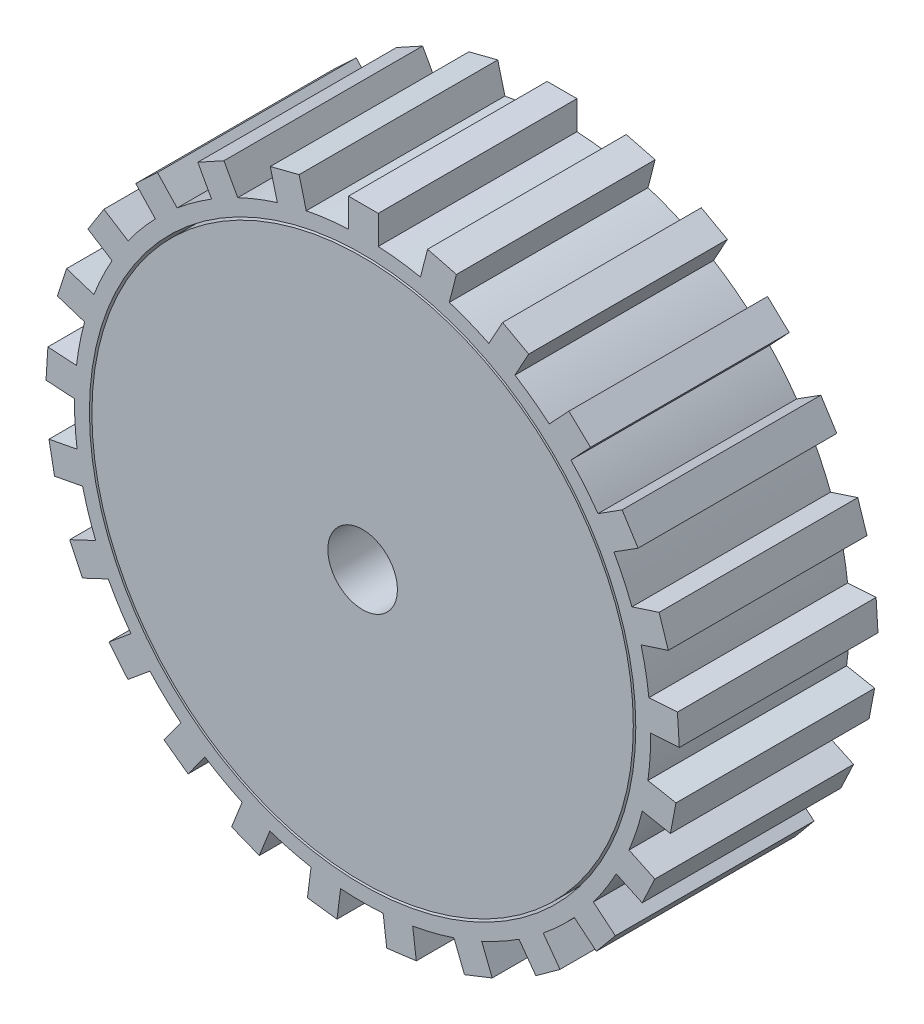
SolidWorks part; units mm, degrees
ref_plane "Front Plane" through (0, 0, 0) normal (0, 0, 1) x (1, 0, 0)
ref_plane "Top Plane" through (0, 0, 0) normal (0, 1, 0) x (1, 0, 0)
ref_plane "Right Plane" through (0, 0, 0) normal (1, 0, 0) x (0, 0, -1)
sketch "Sketch1" plane through (0, 0, 0) normal (0, 0, 1) x (1, 0, 0)
  line L0 (-1.4243, 28.965) -> (-1.4243, 31.8414)
  line L1 (-1.4243, 31.8414) -> (1.5757, 31.8414)
  line L2 (1.5757, 31.8414) -> (1.5757, 28.9572)
  line L3 (9.4448, 30.4492) -> (8.7275, 27.6556)
  line L4 (6.5391, 31.1953) -> (9.4448, 30.4492)
  line L5 (5.8237, 28.4092) -> (6.5391, 31.1953)
  line L6 (16.7205, 27.1438) -> (15.331, 24.6163)
  line L7 (14.0916, 28.589) -> (16.7205, 27.1438)
  line L8 (12.7058, 26.0684) -> (14.0916, 28.589)
  line L9 (22.9456, 22.1328) -> (20.9712, 20.0302)
  line L10 (20.7587, 24.1864) -> (22.9456, 22.1328)
  line L11 (18.7896, 22.0896) -> (20.7587, 24.1864)
  line L12 (27.7289, 15.7311) -> (25.2936, 14.1856)
  line L13 (26.1214, 18.2641) -> (27.7289, 15.7311)
  line L14 (23.6928, 16.7228) -> (26.1214, 18.2641)
  line L15 (30.7699, 8.341) -> (28.0268, 7.4497)
  line L16 (29.8429, 11.1942) -> (30.7699, 8.341)
  line L17 (27.1072, 10.3053) -> (29.8429, 11.1942)
  line L18 (31.8775, 0.4268) -> (28.999, 0.2457)
  line L19 (31.6892, 3.4209) -> (31.8775, 0.4268)
  line L20 (28.8184, 3.2403) -> (31.6892, 3.4209)
  line L21 (30.9822, -7.5142) -> (28.149, -6.9738)
  line L22 (31.5443, -4.5674) -> (30.9822, -7.5142)
  line L23 (28.7188, -4.0284) -> (31.5443, -4.5674)
  line L24 (28.1401, -14.9831) -> (25.5303, -13.7551)
  line L25 (29.4174, -12.2686) -> (28.1401, -14.9831)
  line L26 (26.8148, -11.0439) -> (29.4174, -12.2686)
  line L27 (23.5299, -21.5106) -> (21.3075, -19.6721)
  line L28 (25.4421, -19.199) -> (23.5299, -21.5106)
  line L29 (23.2258, -17.3655) -> (25.4421, -19.199)
  line L30 (17.4412, -26.6864) -> (15.7459, -24.353)
  line L31 (19.8682, -24.923) -> (17.4412, -26.6864)
  line L32 (18.1775, -22.596) -> (19.8682, -24.923)
  line L33 (10.2566, -30.1854) -> (9.1948, -27.5037)
  line L34 (13.0459, -29.0811) -> (10.2566, -30.1854)
  line L35 (11.987, -26.4066) -> (13.0459, -29.0811)
  line L36 (2.4275, -31.7878) -> (2.0661, -28.9263)
  line L37 (5.4039, -31.4118) -> (2.4275, -31.7878)
  line L38 (5.0434, -28.5581) -> (5.4039, -31.4118)
  line L39 (-5.554, -31.3929) -> (-5.1925, -28.5313)
  line L40 (-2.5777, -31.7689) -> (-5.554, -31.3929)
  line L41 (-2.2172, -28.9151) -> (-2.5777, -31.7689)
  line L42 (-13.1866, -29.0254) -> (-12.1249, -26.3436)
  line L43 (-10.3973, -30.1297) -> (-13.1866, -29.0254)
  line L44 (-9.3384, -27.4553) -> (-10.3973, -30.1297)
  line L45 (-19.9907, -24.8341) -> (-18.2953, -22.5007)
  line L46 (-17.5636, -26.5975) -> (-19.9907, -24.8341)
  line L47 (-15.8729, -24.2704) -> (-17.5636, -26.5975)
  line L48 (-25.5386, -19.0824) -> (-23.3162, -17.2439)
  line L49 (-23.6263, -21.394) -> (-25.5386, -19.0824)
  line L50 (-21.41, -19.5605) -> (-23.6263, -21.394)
  line L51 (-29.4819, -12.1317) -> (-26.8721, -10.9037)
  line L52 (-28.2045, -14.8462) -> (-29.4819, -12.1317)
  line L53 (-25.6019, -13.6215) -> (-28.2045, -14.8462)
  line L54 (-31.5727, -4.4187) -> (-28.7395, -3.8783)
  line L55 (-31.0105, -7.3656) -> (-31.5727, -4.4187)
  line L56 (-28.1851, -6.8266) -> (-31.0105, -7.3656)
  line L57 (-31.6797, 3.5719) -> (-28.8011, 3.3908)
  line L58 (-31.868, 0.5778) -> (-31.6797, 3.5719)
  line L59 (-28.9973, 0.3972) -> (-31.868, 0.5778)
  line L60 (-29.7961, 11.3381) -> (-27.053, 10.4468)
  line L61 (-30.7231, 8.4849) -> (-29.7961, 11.3381)
  line L62 (-27.9875, 7.5961) -> (-30.7231, 8.4849)
  line L63 (-26.0403, 18.3919) -> (-23.6051, 16.8464)
  line L64 (-27.6478, 15.8589) -> (-26.0403, 18.3919)
  line L65 (-25.2192, 14.3176) -> (-27.6478, 15.8589)
  line L66 (-20.6483, 24.29) -> (-18.6739, 22.1875)
  line L67 (-22.8353, 22.2364) -> (-20.6483, 24.29)
  line L68 (-20.8662, 20.1396) -> (-22.8353, 22.2364)
  line L69 (-13.959, 28.6619) -> (-12.5695, 26.1344)
  line L70 (-16.5879, 27.2167) -> (-13.959, 28.6619)
  line L71 (-15.2022, 24.696) -> (-16.5879, 27.2167)
  line L72 (-6.3925, 31.2329) -> (-5.6752, 28.4393)
  line L73 (-9.2982, 30.4868) -> (-6.3925, 31.2329)
  line L74 (-8.5829, 27.7008) -> (-9.2982, 30.4868)
  circle A0 centre (0, 0) radius 27.5
  arc A1 (-15.2022, 24.696) -> (-18.6739, 22.1875) centre (0, 0) ccw
  arc A2 (-20.8662, 20.1396) -> (-23.6051, 16.8464) centre (0, 0) ccw
  arc A3 (-25.2192, 14.3176) -> (-27.053, 10.4468) centre (0, 0) ccw
  arc A4 (-8.5829, 27.7008) -> (-12.5695, 26.1344) centre (0, 0) ccw
  arc A5 (-1.4243, 28.965) -> (-5.6752, 28.4393) centre (0, 0) ccw
  arc A6 (5.8237, 28.4092) -> (1.5757, 28.9572) centre (0, 0) ccw
  arc A7 (12.7058, 26.0684) -> (8.7275, 27.6556) centre (0, 0) ccw
  arc A8 (18.7896, 22.0896) -> (15.331, 24.6163) centre (0, 0) ccw
  arc A9 (23.6928, 16.7228) -> (20.9712, 20.0302) centre (0, 0) ccw
  arc A10 (27.1072, 10.3053) -> (25.2936, 14.1856) centre (0, 0) ccw
  arc A11 (28.8184, 3.2403) -> (28.0268, 7.4497) centre (0, 0) ccw
  arc A12 (28.7188, -4.0284) -> (28.999, 0.2457) centre (0, 0) ccw
  arc A13 (26.8148, -11.0439) -> (28.149, -6.9738) centre (0, 0) ccw
  arc A14 (23.2258, -17.3655) -> (25.5303, -13.7551) centre (0, 0) ccw
  arc A15 (18.1775, -22.596) -> (21.3075, -19.6721) centre (0, 0) ccw
  arc A16 (11.987, -26.4066) -> (15.7459, -24.353) centre (0, 0) ccw
  arc A17 (5.0434, -28.5581) -> (9.1948, -27.5037) centre (0, 0) ccw
  arc A18 (-2.2172, -28.9151) -> (2.0661, -28.9263) centre (0, 0) ccw
  arc A19 (-27.9875, 7.5961) -> (-28.8011, 3.3908) centre (0, 0) ccw
  arc A20 (-28.9973, 0.3972) -> (-28.7395, -3.8783) centre (0, 0) ccw
  arc A21 (-28.1851, -6.8266) -> (-26.8721, -10.9037) centre (0, 0) ccw
  arc A22 (-25.6019, -13.6215) -> (-23.3162, -17.2439) centre (0, 0) ccw
  arc A23 (-21.41, -19.5605) -> (-18.2953, -22.5007) centre (0, 0) ccw
  arc A24 (-15.8729, -24.2704) -> (-12.1249, -26.3436) centre (0, 0) ccw
  arc A25 (-9.3384, -27.4553) -> (-5.1925, -28.5313) centre (0, 0) ccw
  point P105 (0, 0)
  dimension "D1" = 55
  dimension "D2" = 25
  dimension "D3" = 3
extrude "Boss-Extrude2" add sketch "Sketch1" along normal blind 20
sketch "Sketch2" plane through (0, 0, 20) normal (0, 0, 1) x (1, 0, 0)
  circle A0 centre (0, 0) radius 27.25
  dimension "D1" = 54.5
extrude "Boss-Extrude5" add sketch "Sketch2" against normal blind 20 separate body
sketch "Sketch3" plane through (0, 0, 0) normal (0, 0, -1) x (-1, 0, 0)
  circle A0 centre (0, 0) radius 12.5
  circle A1 centre (0, 0) radius 3.5
  dimension "D1" = 25
  dimension "D2" = 7
extrude "Cut-Extrude3" cut sketch "Sketch3" against normal through all contours A1
